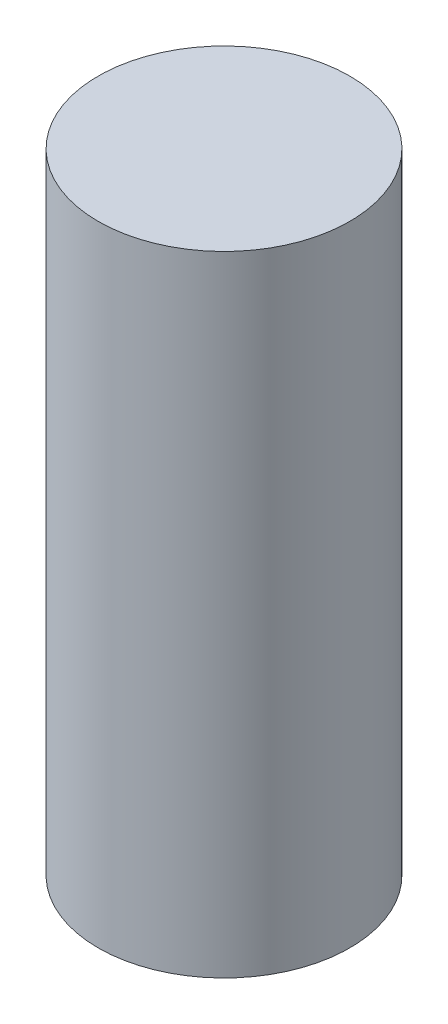
SolidWorks part; units mm, degrees
ref_plane "Front Plane" through (0, 0, 0) normal (0, 0, 1) x (1, 0, 0)
ref_plane "Top Plane" through (0, 0, 0) normal (0, 1, 0) x (1, 0, 0)
ref_plane "Right Plane" through (0, 0, 0) normal (1, 0, 0) x (0, 0, -1)
sketch "Sketch1" plane through (0, 0, 0) normal (0, 1, 0) x (1, 0, 0)
  circle A0 centre (0, 0) radius 3.175
  dimension "D1" = 6.35
extrude "Boss-Extrude1" add sketch "Sketch1" along normal blind 15.875
